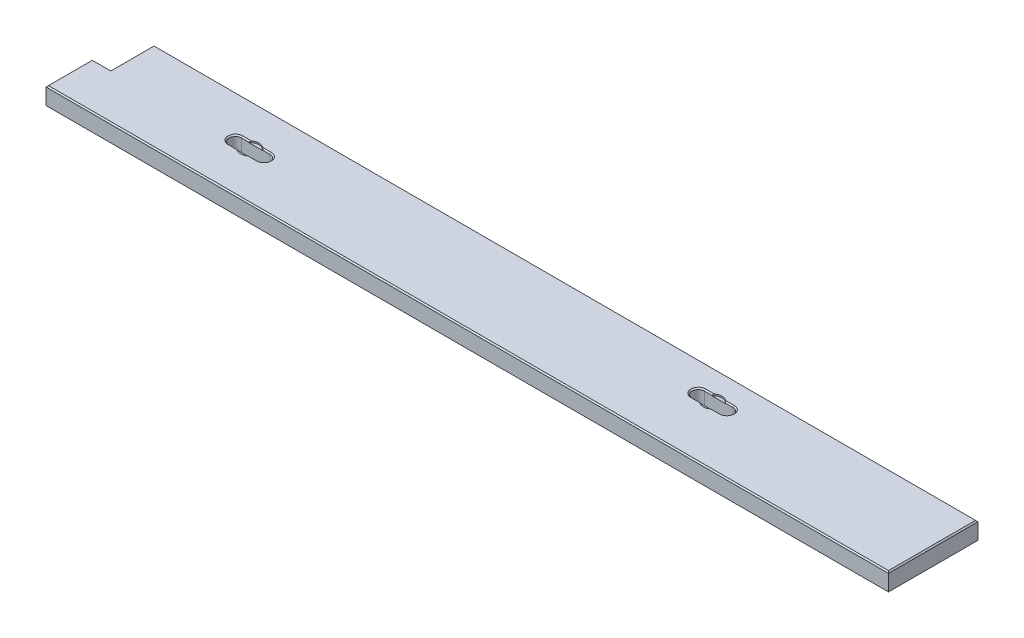
SolidWorks part; units mm, degrees
material "Oak"
ref_plane "Front Plane" through (0, 0, 0) normal (0, 0, 1) x (1, 0, 0)
ref_plane "Top Plane" through (0, 0, 0) normal (0, 1, 0) x (1, 0, 0)
ref_plane "Right Plane" through (0, 0, 0) normal (1, 0, 0) x (0, 0, -1)
sketch "Sketch1" plane through (0, 0, 0) normal (0, 1, 0) x (1, 0, 0)
  line L0 (1181.2651, 135.5661) -> (1240.0153, 135.5661)
  line L1 (0, 0) -> (1695.45, 0)
  line L2 (0, 0) -> (0, 184.15)
  line L3 (0, 184.15) -> (1695.45, 184.15)
  line L4 (1695.45, 0) -> (1695.45, 184.15)
  line L5 (1181.2651, 110.1661) -> (1240.0153, 110.1661)
  line L6 (254, 110.3186) -> (312.7502, 110.3186)
  line L8 (254, 84.9185) -> (312.7502, 84.9185)
  arc A4 (312.7502, 84.9185) -> (312.7502, 110.3186) centre (312.7502, 97.6185) ccw
  arc A5 (254, 110.3186) -> (254, 84.9185) centre (254, 97.6185) ccw
  arc A6 (1240.0153, 110.1661) -> (1240.0153, 135.5661) centre (1240.0153, 122.8661) ccw
  arc A7 (1181.2651, 135.5661) -> (1181.2651, 110.1661) centre (1181.2651, 122.8661) ccw
  point P6 (1240.0153, 135.5661)
  point P14 (312.7502, 110.3186)
  dimension "D7" = 12.7
  dimension "D6" = 1181.2651
  dimension "D9" = 12.7
  dimension "D1" = 184.15
  dimension "D2" = 1695.45
  dimension "D3" = 58.7502
  dimension "D4" = 97.6185
  dimension "D5" = 254
  dimension "D8" = 58.7502
  dimension "D10" = 122.8661
extrude "Boss-Extrude1" add sketch "Sketch1" along normal blind 38.1
sketch "Sketch2" plane through (0, 38.1, 0) normal (0, 1, 0) x (1, 0, 0)
  line L0 (0, 184.15) -> (0, 0) construction
  line L1 (0, 0) -> (-38.1, 0)
  line L2 (0, 0) -> (0, 95.25)
  line L3 (0, 95.25) -> (-38.1, 95.25)
  line L4 (-38.1, 0) -> (-38.1, 95.25)
  dimension "D1" = 38.1
  dimension "D2" = 95.25
extrude "Boss-Extrude3" add sketch "Sketch2" against normal through all
chamfer "Chamfer1" distance 2.54 angle 45 14 edges at (847.725, 38.1, -184.15) (1695.45, 38.1, -92.075) (828.675, 38.1, 0) (0, 38.1, -139.7) (283.3751, 38.1, -110.3186) (283.3751, 38.1, -84.9185) (241.3, 38.1, -97.6185) (325.4502, 38.1, -97.6185) (-38.1, 38.1, -47.625) (-19.05, 38.1, -95.25) (1210.6402, 38.1, -135.5661) (1168.5651, 38.1, -122.8661) (1210.6402, 38.1, -110.1661) (1252.7153, 38.1, -122.8661)
chamfer "Chamfer2" distance 2.54 angle 45 14 edges at (283.3751, 0, -110.3186) (283.3751, 0, -84.9185) (828.675, 0, 0) (1695.45, 0, -92.075) (847.725, 0, -184.15) (0, 0, -139.7) (241.3, 0, -97.6185) (325.4502, 0, -97.6185) (-19.05, 0, -95.25) (-38.1, 0, -47.625) (1168.5651, 0, -122.8661) (1210.6402, 0, -135.5661) (1252.7153, 0, -122.8661) (1210.6402, 0, -110.1661)
sketch "Sketch3" plane through (0, 38.1, 0) normal (0, 1, 0) x (1, 0, 0)
  line L0 (254, 97.6185) -> (312.7502, 97.6185) construction
  line L1 (1181.2651, 122.8661) -> (1240.0153, 122.8661) construction
  circle A0 centre (1210.6402, 122.8661) radius 19.05
  circle A1 centre (283.3751, 97.6185) radius 19.05
  dimension "D1" = 38.1
  dimension "D2" = 38.1
extrude "Cut-Extrude1" cut sketch "Sketch3" against normal blind 3.175
